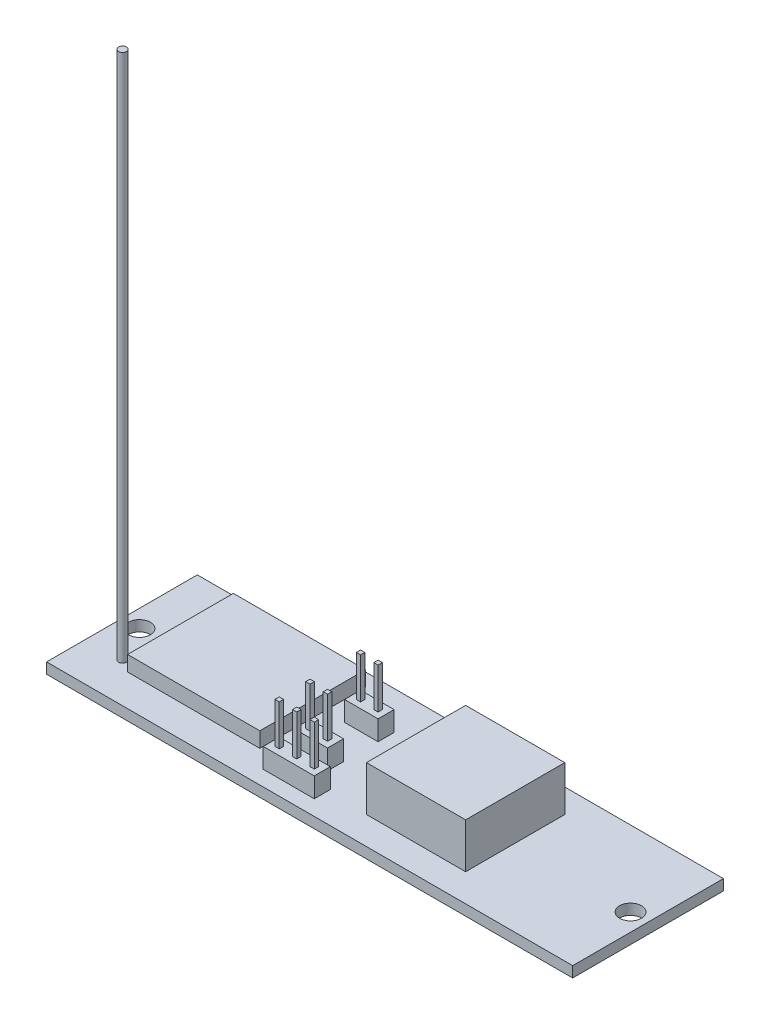
SolidWorks part; units mm, degrees
material "PVC Rigid"
ref_plane "Front Plane" through (0, 0, 0) normal (0, 0, 1) x (1, 0, 0)
ref_plane "Top Plane" through (0, 0, 0) normal (0, 1, 0) x (1, 0, 0)
ref_plane "Right Plane" through (0, 0, 0) normal (1, 0, 0) x (0, 0, -1)
sketch "Sketch1" plane through (0, 0, 0) normal (0, 1, 0) x (1, 0, 0)
  line L0 (0, 0) -> (79.57, 0)
  line L1 (79.57, 0) -> (79.57, 22.8)
  line L2 (79.57, 22.8) -> (0, 22.8)
  line L3 (0, 22.8) -> (0, 0)
  line L4 (0, 11.4) -> (1, 11.4) construction
  line L5 (79.57, 11.4) -> (78.57, 11.4) construction
  circle A0 centre (2.65, 11.4) radius 1.65
  circle A1 centre (76.92, 11.4) radius 1.65
  dimension "D3" = 3.3
  dimension "D5" = 11.4
  dimension "D6" = 3.3
  dimension "D1" = 79.57
  dimension "D2" = 22.8
  dimension "D4" = 2.65
  dimension "D7" = 2.65
  dimension "D8" = 11.4
extrude "Boss-Extrude2" add sketch "Sketch1" along normal blind 1.62 contours L3 L0 L1 L2 | A0 | A1
ref_plane "Plane1" through (0, 1.62, 0) normal (0, 1, 0) x (1, 0, 0)
sketch "Sketch2" plane through (0, 1.62, 0) normal (0, 1, 0) x (1, 0, 0)
  line L0 (59.18, 4.2) -> (44.18, 4.2)
  line L1 (44.18, 4.2) -> (44.18, 19.2)
  line L2 (44.18, 19.2) -> (59.18, 19.2)
  line L3 (59.18, 19.2) -> (59.18, 4.2)
  line L4 (79.57, 0) -> (79.57, 22.8) construction
  line L6 (0, 0) -> (79.57, 0) construction
  dimension "D1" = 20.39
  dimension "D2" = 15
  dimension "D3" = 15
  dimension "D4" = 4.2
extrude "Boss-Extrude3" add sketch "Sketch2" along normal blind 6.8
sketch "Sketch3" plane through (0, 1.62, 0) normal (0, 1, 0) x (1, 0, 0)
  line L0 (31.34, 3.85) -> (31.34, 3.2)
  line L1 (31.34, 3.2) -> (31.99, 3.2)
  line L2 (31.99, 3.2) -> (31.99, 3.85)
  line L3 (31.99, 3.85) -> (31.34, 3.85)
  line L28 (0, 22.8) -> (0, 0) construction
  line L29 (0, 0) -> (79.57, 0) construction
  line L30 (33.99, 3.85) -> (33.99, 3.2)
  line L31 (33.99, 3.2) -> (34.64, 3.2)
  line L32 (34.64, 3.2) -> (34.64, 3.85)
  line L33 (34.64, 3.85) -> (33.99, 3.85)
  line L34 (36.64, 3.85) -> (36.64, 3.2)
  line L35 (36.64, 3.2) -> (37.29, 3.2)
  line L36 (37.29, 3.2) -> (37.29, 3.85)
  line L37 (37.29, 3.85) -> (36.64, 3.85)
  line L38 (31.34, 8.5) -> (31.34, 7.85)
  line L39 (31.34, 7.85) -> (31.99, 7.85)
  line L40 (31.99, 7.85) -> (31.99, 8.5)
  line L41 (31.99, 8.5) -> (31.34, 8.5)
  line L42 (33.99, 8.5) -> (33.99, 7.85)
  line L43 (33.99, 7.85) -> (34.64, 7.85)
  line L44 (34.64, 7.85) -> (34.64, 8.5)
  line L45 (34.64, 8.5) -> (33.99, 8.5)
  line L46 (31.34, 16.15) -> (31.34, 15.5)
  line L47 (31.34, 15.5) -> (31.99, 15.5)
  line L48 (31.99, 15.5) -> (31.99, 16.15)
  line L49 (31.99, 16.15) -> (31.34, 16.15)
  line L50 (33.99, 16.15) -> (33.99, 15.5)
  line L51 (33.99, 15.5) -> (34.64, 15.5)
  line L52 (34.64, 15.5) -> (34.64, 16.15)
  line L53 (34.64, 16.15) -> (33.99, 16.15)
  dimension "D1" = 0.65
  dimension "D2" = 0.65
  dimension "D3" = 31.34
  dimension "D4" = 3.2
  dimension "D5" = 3
  dimension "D6" = 2
  dimension "D7" = 4
  dimension "D8" = 0.65
  dimension "D9" = 0.65
  dimension "D10" = 7
extrude "Boss-Extrude4" add sketch "Sketch3" along normal blind 9.16
sketch "Sketch4" plane through (0, 1.62, 0) normal (0, 1, 0) x (1, 0, 0)
  line L0 (30.455, 4.735) -> (30.455, 2.315)
  line L1 (30.455, 2.315) -> (38.175, 2.315)
  line L2 (38.175, 2.315) -> (38.175, 4.735)
  line L3 (38.175, 4.735) -> (30.455, 4.735)
  line L4 (31.34, 3.85) -> (31.34, 3.2) construction
  line L5 (31.99, 3.85) -> (31.34, 3.85) construction
  line L6 (37.29, 3.2) -> (37.29, 3.85) construction
  line L7 (30.455, 6.965) -> (30.455, 9.385)
  line L8 (30.455, 9.385) -> (35.525, 9.385)
  line L9 (35.525, 9.385) -> (35.525, 6.965)
  line L10 (35.525, 6.965) -> (30.455, 6.965)
  line L11 (30.455, 14.611) -> (30.455, 17.035)
  line L12 (30.455, 17.035) -> (35.525, 17.035)
  line L13 (35.525, 17.035) -> (35.525, 14.611)
  line L14 (35.525, 14.611) -> (30.455, 14.611)
  line L15 (31.99, 8.5) -> (31.34, 8.5) construction
  line L16 (31.34, 7.85) -> (31.99, 7.85) construction
  line L17 (34.64, 7.85) -> (34.64, 8.5) construction
  line L18 (31.34, 15.5) -> (31.99, 15.5) construction
  line L20 (31.99, 16.15) -> (31.34, 16.15) construction
  point P9 (31.34, 3.525)
  dimension "D1" = 0.885
  dimension "D2" = 2.42
  dimension "D3" = 0.885
  dimension "D4" = 0.885
  dimension "D5" = 0.885
  dimension "D6" = 0.885
  dimension "D7" = 0.885
  dimension "D8" = 0.889
  dimension "D9" = 0.885
extrude "Boss-Extrude5" add sketch "Sketch4" along normal blind 3
sketch "Sketch5" plane through (0, 1.62, 0) normal (0, 1, 0) x (1, 0, 0)
  line L0 (7.45, 20.8) -> (7.45, 4.8)
  line L1 (7.45, 4.8) -> (27.45, 4.8)
  line L2 (27.45, 4.8) -> (27.45, 20.8)
  line L3 (27.45, 20.8) -> (7.45, 20.8)
  line L4 (0, 22.8) -> (0, 0) construction
  line L5 (79.57, 22.8) -> (0, 22.8) construction
  dimension "D1" = 16
  dimension "D2" = 20
  dimension "D3" = 7.45
  dimension "D4" = 2
extrude "Boss-Extrude6" add sketch "Sketch5" along normal blind 2.3
sketch "Sketch6" plane through (0, 1.62, 0) normal (0, 1, 0) x (1, 0, 0)
  line L0 (0, 0) -> (79.57, 0) construction
  line L1 (0, 22.8) -> (0, 0) construction
  circle A0 centre (5.5, 6) radius 0.45
  dimension "D3" = 0.9
  dimension "D1" = 6
  dimension "D2" = 5.5
extrude "Hole for antenna" cut sketch "Sketch6" against normal blind 2.8
sketch "Sketch7" plane through (0, 1.62, 0) normal (0, 1, 0) x (1, 0, 0)
  circle A0 centre (5.5, 6) radius 0.6
  dimension "D1" = 1.2
extrude "Boss-Extrude7" add sketch "Sketch7" along normal blind 80
